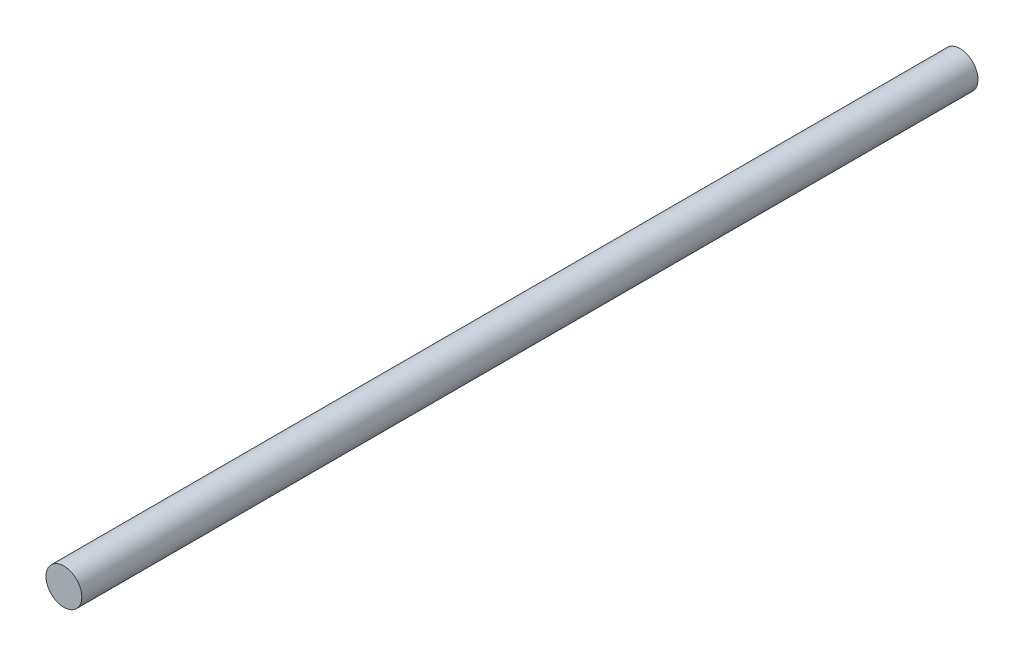
SolidWorks part; units mm, degrees
ref_plane "正面" through (0, 0, 0) normal (0, 0, 1) x (1, 0, 0)
ref_plane "平面" through (0, 0, 0) normal (0, 1, 0) x (1, 0, 0)
ref_plane "右側面" through (0, 0, 0) normal (1, 0, 0) x (0, 0, -1)
sketch "ｽｹｯﾁ1" plane through (0, 0, 0) normal (0, 0, 1) x (1, 0, 0)
  circle A0 centre (0, 0) radius 3
  dimension "D1" = 6
extrude "ﾎﾞｽ - 押し出し1" add sketch "ｽｹｯﾁ1" along normal blind 150
